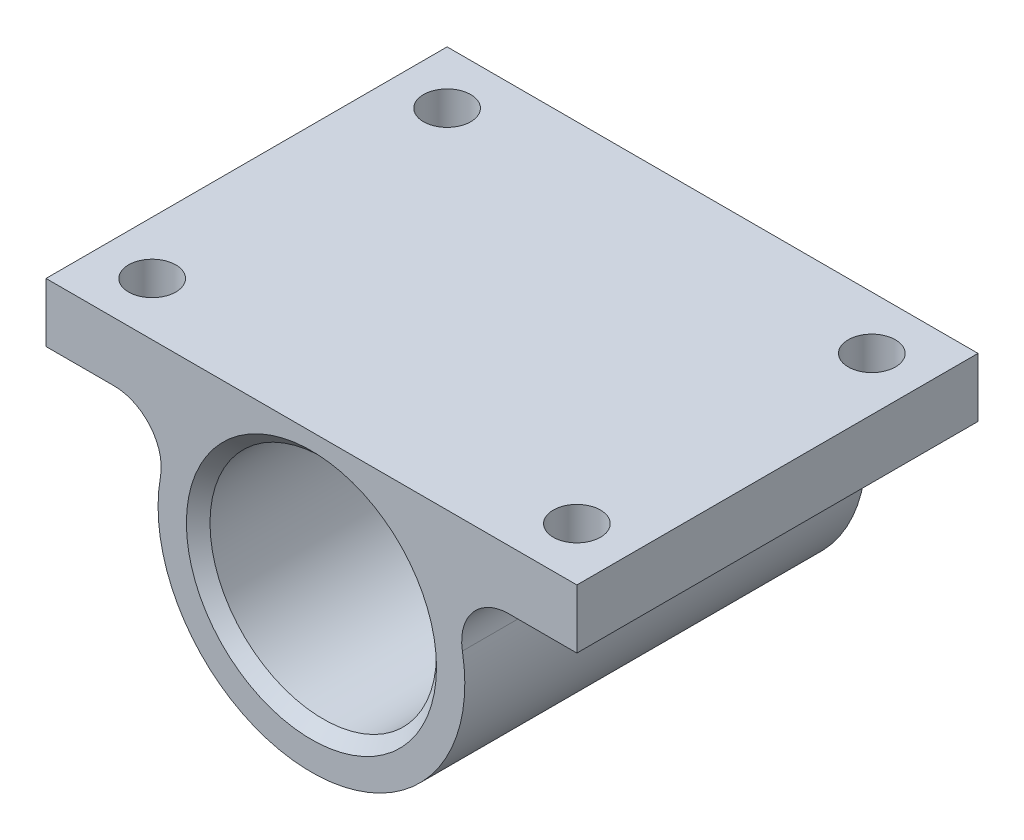
SolidWorks part; units mm, degrees
ref_plane "Front Plane" through (0, 0, 0) normal (0, 0, 1) x (1, 0, 0)
ref_plane "Top Plane" through (0, 0, 0) normal (0, 1, 0) x (1, 0, 0)
ref_plane "Right Plane" through (0, 0, 0) normal (1, 0, 0) x (0, 0, -1)
sketch "Sketch1" plane through (0, 0, 0) normal (0, 0, 1) x (1, 0, 0)
  line L0 (16.7332, 7) -> (22.5, 7)
  line L1 (-22.5, 12) -> (22.5, 12)
  line L2 (-22.5, 12) -> (-22.5, 7)
  line L3 (-22.5, 7) -> (-16.7332, 7)
  line L4 (22.5, 12) -> (22.5, 7)
  line L5 (0, 0) -> (0, 12) construction
  circle A0 centre (0, 0) radius 9.6
  arc A1 (-12.796, 2.2941) -> (12.796, 2.2941) centre (0, 0) ccw
  arc A2 (12.796, 2.2941) -> (16.7332, 7) centre (16.7332, 3) cw
  arc A3 (-12.796, 2.2941) -> (-16.7332, 7) centre (-16.7332, 3) ccw
  point P12 (10.9545, 7)
  dimension "D1" = 19.2
  dimension "D2" = 13
  dimension "D6" = 4
  dimension "D3" = 12
  dimension "D4" = 45
  dimension "D5" = 5
extrude "Boss-Extrude1" add sketch "Sketch1" along normal blind 34
sketch "Sketch2" plane through (0, 12, 0) normal (0, 1, 0) x (1, 0, 0)
  line L0 (-18, -29.5) -> (18, -4.5) construction
  line L1 (0, -17) -> (0, 0) construction
  line L2 (0, -17) -> (-22.5, -17) construction
  line L3 (-22.5, -34) -> (-22.5, 0) construction
  circle A0 centre (-18, -29.5) radius 2
  circle A1 centre (18, -29.5) radius 2
  circle A2 centre (18, -4.5) radius 2
  circle A3 centre (-18, -4.5) radius 2
  dimension "D3" = 4
  dimension "D1" = 25
  dimension "D2" = 36
extrude "Cut-Extrude1" cut sketch "Sketch2" against normal blind 34
sketch "Sketch3" plane through (0, 7, 0) normal (0, -1, 0) x (1, 0, 0)
  circle A0 centre (-18, 29.5) radius 4
  circle A1 centre (-18, 4.5) radius 4
  circle A2 centre (18, 4.5) radius 4
  circle A3 centre (18, 29.5) radius 4
  dimension "D1" = 8
extrude "Cut-Extrude2" cut sketch "Sketch3" along normal blind 34
sketch "Sketch4" plane through (0, 0, 0) normal (0, 0, -1) x (-1, 0, 0)
  circle A0 centre (0, 0) radius 8.5
  circle A1 centre (0, 0) radius 9.6
  circle A2 centre (0, 0) radius 9.6 construction
  dimension "D1" = 17
extrude "Boss-Extrude2" add sketch "Sketch4" against normal blind 2
chamfer "Chamfer1" distance 1 angle 45 1 edges at (9.6, 0, 34)
